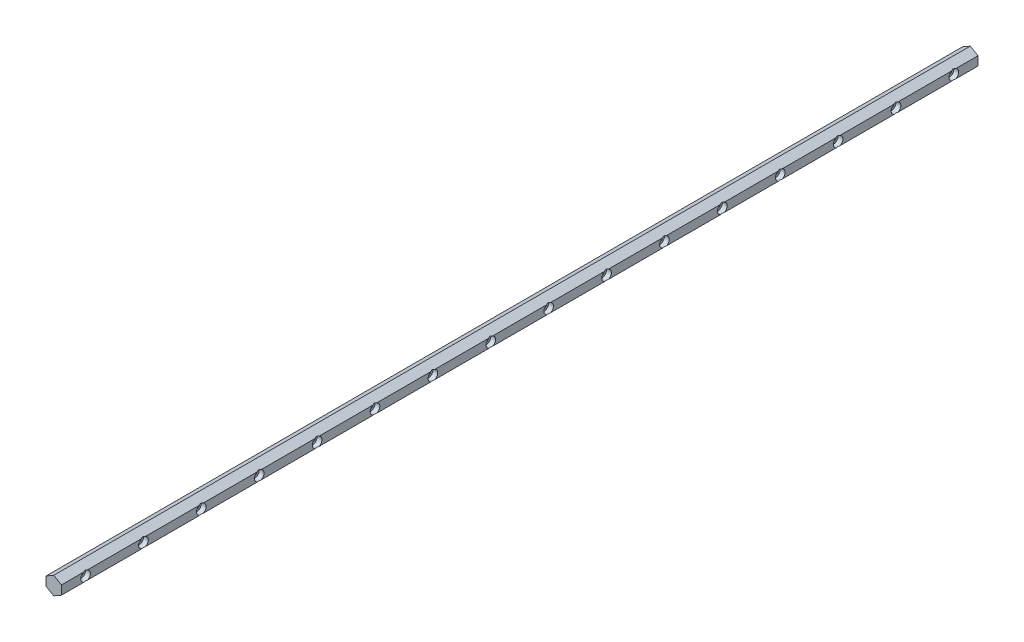
SolidWorks part; units mm, degrees
material "AISI 304"
ref_plane "Front Plane" through (0, 0, 0) normal (0, 0, 1) x (1, 0, 0)
ref_plane "Top Plane" through (0, 0, 0) normal (0, 1, 0) x (1, 0, 0)
ref_plane "Right Plane" through (0, 0, 0) normal (1, 0, 0) x (0, 0, -1)
sketch "Sketch1" plane through (0, 0, 0) normal (0, 0, 1) x (1, 0, 0)
  line L1 (0, -9.2376) -> (8, -4.6188)
  line L2 (8, -4.6188) -> (8, 4.6188)
  line L3 (8, 4.6188) -> (0, 9.2376)
  line L4 (0, 9.2376) -> (-8, 4.6188)
  line L5 (-8, 4.6188) -> (-8, -4.6188)
  line L6 (-8, -4.6188) -> (0, -9.2376)
  circle A0 centre (0, 0) radius 8 construction
  dimension "D1" = 16
extrude "Boss-Extrude1" add sketch "Sketch1" along normal blind 950
sketch "Sketch2" plane through (8, 0, 0) normal (1, 0, 0) x (0, 0, -1)
  line L0 (-950, -4.6188) -> (-950, 4.6188) construction
  line L1 (-950, 0) -> (0, 0) construction
  point P9 (-925, 0)
  dimension "D1" = 25
hole_wizard "CBORE for M5 Socket Head Cap Screw2" positions "3DSketch3" profile "Sketch5" counterbore size "M5" standard "IS" end condition through all
sketch3d "3DSketch3"
  point P0 (8, 0, 925)
sketch "Sketch5" plane through (8, 0, 925) normal (0, 1, 0) x (0, 0, -1)
  line L0 (0, 0) -> (0, 16)
  line L1 (0, 16) -> (2.75, 16)
  line L3 (2.75, 16) -> (2.75, 5)
  line L4 (2.75, 5) -> (5, 5)
  line L5 (5, 5) -> (5, 0)
  line L7 (5, 0) -> (0, 0)
  line L11 (0, -6.35) -> (0, 107.95) construction
  dimension "Thru Hole Dia." = 5.5
  dimension "Thru Hole Depth" = 16
  dimension "C'Bore Dia." = 10
  dimension "C'Bore Depth" = 5
pattern_linear "LPattern1" count 16 spacing 60 along (0, 0, -1) of "CBORE for M5 Socket Head Cap Screw2"
equation "\"rail_length\"=950"
equation "\"D1@Boss-Extrude1\"=\"rail_length\""
equation "\"holeoffset\"=25"
equation "\"holespacing\"=60"
equation "\"D1@Sketch2\"=\"holeoffset\""
equation "\"D3@LPattern1\"=\"holespacing\""
